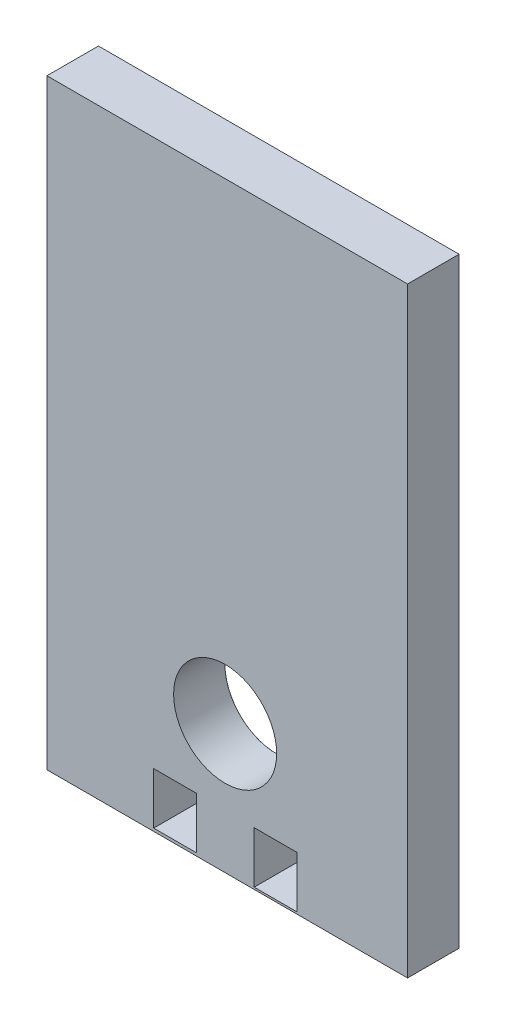
SolidWorks part; units mm, degrees
ref_plane "Front Plane" through (0, 0, 0) normal (0, 0, 1) x (1, 0, 0)
ref_plane "Top Plane" through (0, 0, 0) normal (0, 1, 0) x (1, 0, 0)
ref_plane "Right Plane" through (0, 0, 0) normal (1, 0, 0) x (0, 0, -1)
sketch "Sketch1" plane through (0, 0, 0) normal (0, 0, 1) x (1, 0, 0)
  line L1 (-30.8498, 104.8892) -> (11.1502, 104.8892)
  line L2 (-30.8498, 104.8892) -> (-30.8498, 34.8892)
  line L3 (-30.8498, 34.8892) -> (11.1502, 34.8892)
  line L4 (11.1502, 104.8892) -> (11.1502, 34.8892)
  line L5 (-30.8498, 104.8892) -> (11.1502, 34.8892) construction
  line L6 (-30.8498, 34.8892) -> (11.1502, 104.8892) construction
  point P0 (-9.8498, 69.8892)
extrude "Boss-Extrude1" add sketch "Sketch1" along normal blind 6
sketch "Sketch2" plane through (0, 0, 0) normal (0, 0, 1) x (1, 0, 0)
  line L12 (-1.7113, 35.1205) -> (-1.7113, 41.1205)
  line L13 (-1.7113, 41.1205) -> (-6.7113, 41.1205)
  line L14 (-6.7113, 41.1205) -> (-6.7113, 35.1205)
  line L15 (-6.7113, 35.1205) -> (-1.7113, 35.1205)
  line L16 (-18.4136, 35.2244) -> (-18.4136, 41.2244)
  line L17 (-18.4136, 41.2244) -> (-13.4136, 41.2244)
  line L18 (-13.4136, 41.2244) -> (-13.4136, 35.2244)
  line L19 (-13.4136, 35.2244) -> (-18.4136, 35.2244)
extrude "Cut-Extrude1" cut sketch "Sketch2" along normal blind 9
hole_wizard "Ø12.0mm Dowel Hole1" positions "Sketch5" profile "Sketch6" hole size "Ø12.0" standard "GB"
sketch "Sketch5" plane through (0, 0, 0) normal (0, 0, -1) x (-1, 0, 0)
  point P0 (10.0966, 49.8984)
sketch "Sketch6" plane through (-10.0966, 49.8984, 0) normal (1, 0, 0) x (0, 1, 0)
  line L0 (0, 0) -> (0, 53.6052)
  line L1 (0, 53.6052) -> (6, 50)
  line L2 (6, 50) -> (6, 0.025)
  line L3 (6, 0.025) -> (6.025, 0)
  line L5 (6.025, 0) -> (0, 0)
  line L6 (-6, 0.025) -> (-6.025, 0) construction
  line L10 (0, 53.6052) -> (-6, 50) construction
  line L11 (0, -6.35) -> (0, 107.95) construction
  dimension "Hole Dia." = 12
  dimension "Hole Depth" = 50
  dimension "Near C'Sink Dia." = 12.05
  dimension "Near C'Sink Angle" = 90
  dimension "Drill Angle" = 118
